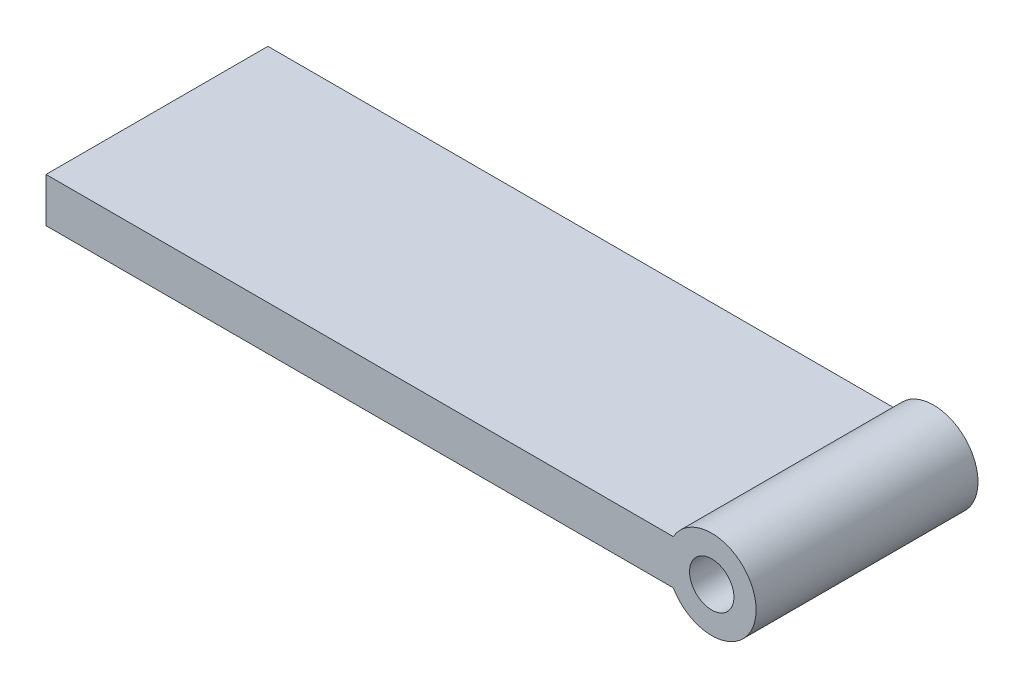
SolidWorks part; units mm, degrees
ref_plane "Front Plane" through (0, 0, 0) normal (0, 0, 1) x (1, 0, 0)
ref_plane "Top Plane" through (0, 0, 0) normal (0, 1, 0) x (1, 0, 0)
ref_plane "Right Plane" through (0, 0, 0) normal (1, 0, 0) x (0, 0, -1)
sketch "Sketch1" plane through (0, 0, 0) normal (0, 1, 0) x (1, 0, 0)
  line L1 (0, 0) -> (-150, 0)
  line L2 (0, 0) -> (0, 50)
  line L3 (0, 50) -> (-150, 50)
  line L4 (-150, 0) -> (-150, 50)
  dimension "D1" = 50
  dimension "D2" = 150
extrude "Boss-Extrude1" add sketch "Sketch1" along normal blind 10
sketch "Sketch2" plane through (0, 0, 0) normal (0, 0, 1) x (1, 0, 0)
  line L0 (0, 10) -> (0, 0) construction
  circle A0 centre (0, 5) radius 10
  dimension "D1" = 20
extrude "Boss-Extrude2" add sketch "Sketch2" against normal through all
sketch "Sketch3" plane through (0, 0, 0) normal (0, 0, 1) x (1, 0, 0)
  circle A0 centre (0, 5) radius 5
  arc A1 (-8.6603, 0) -> (-8.6603, 10) centre (0, 5) ccw construction
  dimension "D1" = 10
extrude "Cut-Extrude1" cut sketch "Sketch3" against normal through all
